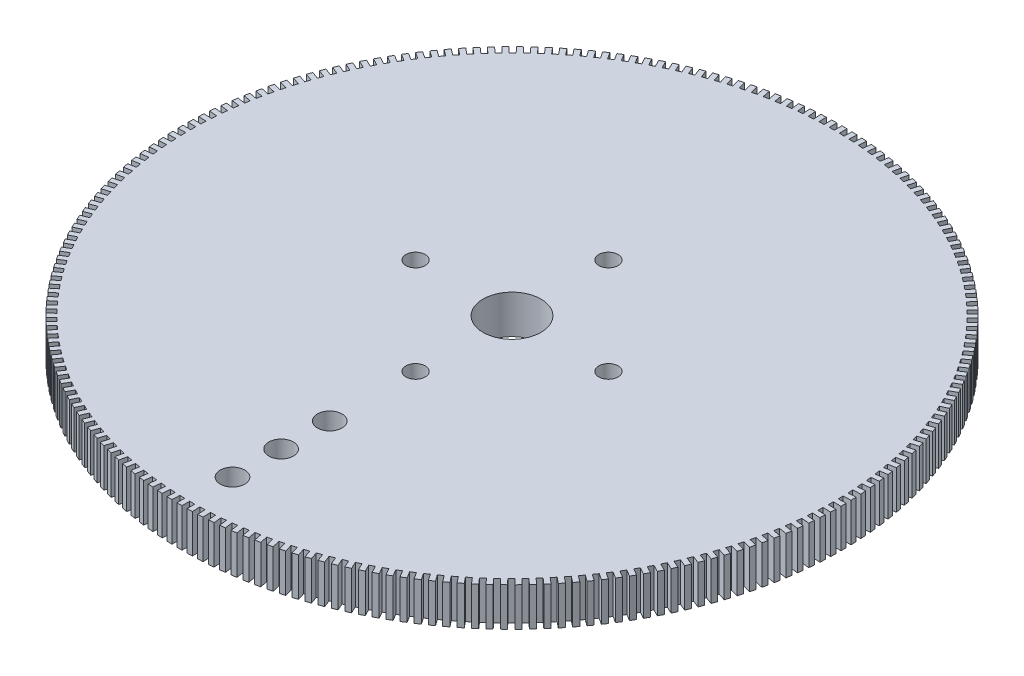
SolidWorks part; units mm, degrees
ref_plane "前基準面" through (0, 0, 0) normal (0, 0, 1) x (1, 0, 0)
ref_plane "上基準面" through (0, 0, 0) normal (0, 1, 0) x (1, 0, 0)
ref_plane "右基準面" through (0, 0, 0) normal (1, 0, 0) x (0, 0, -1)
sketch "草圖1" plane through (0, 0, 0) normal (0, 1, 0) x (1, 0, 0)
  circle A0 centre (0, 0) radius 54.229
  dimension "D1" = 108.458
extrude "填料-伸長1" add sketch "草圖1" along normal blind 6.35
sketch "草圖2" plane through (0, 6.35, 0) normal (0, 1, 0) x (1, 0, 0)
  circle A0 centre (0, 0) radius 4.7625
  circle A1 centre (-15.875, 0) radius 1.5875
  circle A2 centre (15.875, 0) radius 1.5875
  circle A3 centre (0, 15.875) radius 1.5875
  circle A4 centre (0, -15.875) radius 1.5875
  dimension "D1" = 9.525
  dimension "D2" = 3.175
  dimension "D3" = 3.175
  dimension "D4" = 3.175
  dimension "D5" = 3.175
  dimension "D6" = 15.875
  dimension "D7" = 15.875
  dimension "D8" = 15.875
  dimension "D9" = 15.875
extrude "除料-伸長1" cut sketch "草圖2" against normal blind 6.35
sketch "草圖4" plane through (0, 6.35, 0) normal (0, 1, 0) x (1, 0, 0)
  line L0 (0, 0) -> (-100.747, 10.3776) construction
  line L1 (0, 0) -> (-66.515, 6.3317) construction
  line L2 (0, 0) -> (-69.3079, 7.6816) construction
  line L3 (-52.7207, 5.0186) -> (-54.6004, 5.1975)
  line L4 (-54.6004, 5.1975) -> (-54.5069, 6.0411)
  line L5 (-54.5069, 6.0411) -> (-52.6367, 5.8339)
  line L6 (-52.5391, 6.6558) -> (-54.4123, 6.8931)
  line L7 (-54.4123, 6.8931) -> (-54.2926, 7.7334)
  line L8 (-54.2926, 7.7334) -> (-52.4298, 7.468)
  line L9 (-52.3067, 8.2865) -> (-54.1716, 8.582)
  line L10 (-54.1716, 8.582) -> (-54.0259, 9.4181)
  line L11 (-54.0259, 9.4181) -> (-52.1722, 9.095)
  line L12 (-52.0237, 9.9092) -> (-53.8785, 10.2626)
  line L13 (-53.8785, 10.2626) -> (-53.7068, 11.0938)
  line L14 (-53.7068, 11.0938) -> (-51.8641, 10.7131)
  line L15 (-51.6903, 11.5224) -> (-53.5333, 11.9332)
  line L16 (-53.5333, 11.9332) -> (-53.3358, 12.7587)
  line L17 (-53.3358, 12.7587) -> (-51.5058, 12.3209)
  line L18 (-51.307, 13.1244) -> (-53.1363, 13.5923)
  line L19 (-53.1363, 13.5923) -> (-52.9133, 14.4113)
  line L20 (-52.9133, 14.4113) -> (-51.0977, 13.9168)
  line L21 (-50.874, 14.7137) -> (-52.6879, 15.2383)
  line L22 (-52.6879, 15.2383) -> (-52.4395, 16.0499)
  line L23 (-52.4395, 16.0499) -> (-50.6402, 15.4992)
  line L24 (-50.3918, 16.2887) -> (-52.1885, 16.8695)
  line L25 (-52.1885, 16.8695) -> (-51.915, 17.673)
  line L26 (-51.915, 17.673) -> (-50.1337, 17.0666)
  line L27 (-49.8608, 17.848) -> (-51.6386, 18.4844)
  line L28 (-51.6386, 18.4844) -> (-51.3402, 19.279)
  line L29 (-51.3402, 19.279) -> (-49.5787, 18.6175)
  line L30 (-49.2817, 19.39) -> (-51.0388, 20.0814)
  line L31 (-51.0388, 20.0814) -> (-50.7158, 20.8663)
  line L32 (-50.7158, 20.8663) -> (-48.9757, 20.1504)
  line L33 (-48.6548, 20.9133) -> (-50.3895, 21.659)
  line L34 (-50.3895, 21.659) -> (-50.0423, 22.4335)
  line L35 (-50.0423, 22.4335) -> (-48.3253, 21.6638)
  line L36 (-47.9809, 22.4164) -> (-49.6916, 23.2156)
  line L37 (-49.6916, 23.2156) -> (-49.3205, 23.9789)
  line L38 (-49.3205, 23.9789) -> (-47.6282, 23.1562)
  line L39 (-47.2605, 23.8977) -> (-48.9455, 24.7498)
  line L40 (-48.9455, 24.7498) -> (-48.5509, 25.5012)
  line L41 (-48.5509, 25.5012) -> (-46.885, 24.6262)
  line L42 (-46.4944, 25.356) -> (-48.1521, 26.26)
  line L43 (-48.1521, 26.26) -> (-47.7343, 26.9988)
  line L44 (-47.7343, 26.9988) -> (-46.0965, 26.0724)
  line L45 (-45.6834, 26.7897) -> (-47.3122, 27.7448)
  line L46 (-47.3122, 27.7448) -> (-46.8715, 28.4703)
  line L47 (-46.8715, 28.4703) -> (-45.2633, 27.4934)
  line L48 (-44.8281, 28.1974) -> (-46.4264, 29.2028)
  line L49 (-46.4264, 29.2028) -> (-45.9634, 29.9142)
  line L50 (-45.9634, 29.9142) -> (-44.3864, 28.8878)
  line L51 (-43.9295, 29.578) -> (-45.4958, 30.6325)
  line L52 (-45.4958, 30.6325) -> (-45.0109, 31.3292)
  line L53 (-45.0109, 31.3292) -> (-43.4665, 30.2542)
  line L54 (-42.9884, 30.9298) -> (-44.5211, 32.0326)
  line L55 (-44.5211, 32.0326) -> (-44.0148, 32.7138)
  line L56 (-44.0148, 32.7138) -> (-42.5046, 31.5914)
  line L57 (-42.0057, 32.2518) -> (-43.5033, 33.4017)
  line L58 (-43.5033, 33.4017) -> (-42.9761, 34.0669)
  line L59 (-42.9761, 34.0669) -> (-41.5015, 32.898)
  line L60 (-40.9823, 33.5426) -> (-42.4435, 34.7385)
  line L61 (-42.4435, 34.7385) -> (-41.8958, 35.387)
  line L62 (-41.8958, 35.387) -> (-40.4583, 34.1728)
  line L63 (-39.9193, 34.8009) -> (-41.3426, 36.0417)
  line L64 (-41.3426, 36.0417) -> (-40.775, 36.6728)
  line L65 (-40.775, 36.6728) -> (-39.376, 35.4145)
  line L66 (-38.8177, 36.0256) -> (-40.2017, 37.31)
  line L67 (-40.2017, 37.31) -> (-39.6148, 37.9231)
  line L68 (-39.6148, 37.9231) -> (-38.2556, 36.622)
  line L69 (-37.6785, 37.2154) -> (-39.0219, 38.5422)
  line L70 (-39.0219, 38.5422) -> (-38.4162, 39.1368)
  line L71 (-38.4162, 39.1368) -> (-37.0981, 37.794)
  line L72 (-36.5029, 38.3692) -> (-37.8044, 39.7372)
  line L73 (-37.8044, 39.7372) -> (-37.1805, 40.3126)
  line L74 (-37.1805, 40.3126) -> (-35.9048, 38.9295)
  line L75 (-35.292, 39.4858) -> (-36.5503, 40.8937)
  line L76 (-36.5503, 40.8937) -> (-35.9088, 41.4494)
  line L77 (-35.9088, 41.4494) -> (-34.6767, 40.0273)
  line L78 (-34.0469, 40.5643) -> (-35.2608, 42.0106)
  line L79 (-35.2608, 42.0106) -> (-34.6023, 42.5461)
  line L80 (-34.6023, 42.5461) -> (-33.4151, 41.0863)
  line L81 (-32.7689, 41.6035) -> (-33.9373, 43.0869)
  line L82 (-33.9373, 43.0869) -> (-33.2624, 43.6017)
  line L83 (-33.2624, 43.6017) -> (-32.1212, 42.1057)
  line L84 (-31.4592, 42.6025) -> (-32.5808, 44.1215)
  line L85 (-32.5808, 44.1215) -> (-31.8903, 44.6151)
  line L86 (-31.8903, 44.6151) -> (-30.7961, 43.0843)
  line L87 (-30.119, 43.5603) -> (-31.1929, 45.1134)
  line L88 (-31.1929, 45.1134) -> (-30.4874, 45.5853)
  line L89 (-30.4874, 45.5853) -> (-29.4413, 44.0212)
  line L90 (-28.7498, 44.4759) -> (-29.7748, 46.0617)
  line L91 (-29.7748, 46.0617) -> (-29.0549, 46.5114)
  line L92 (-29.0549, 46.5114) -> (-28.058, 44.9155)
  line L93 (-27.3527, 45.3485) -> (-28.3279, 46.9654)
  line L94 (-28.3279, 46.9654) -> (-27.5944, 47.3925)
  line L95 (-27.5944, 47.3925) -> (-26.6476, 45.7664)
  line L96 (-25.9291, 46.1772) -> (-26.8536, 47.8237)
  line L97 (-26.8536, 47.8237) -> (-26.1071, 48.2277)
  line L98 (-26.1071, 48.2277) -> (-25.2114, 46.573)
  line L99 (-24.4804, 46.9613) -> (-25.3533, 48.6357)
  line L100 (-25.3533, 48.6357) -> (-24.5946, 49.0163)
  line L101 (-24.5946, 49.0163) -> (-23.7508, 47.3345)
  line L102 (-23.0081, 47.6999) -> (-23.8284, 49.4006)
  line L103 (-23.8284, 49.4006) -> (-23.0583, 49.7575)
  line L104 (-23.0583, 49.7575) -> (-22.2672, 48.0503)
  line L105 (-21.5135, 48.3924) -> (-22.2806, 50.1178)
  line L106 (-22.2806, 50.1178) -> (-21.4997, 50.4505)
  line L107 (-21.4997, 50.4505) -> (-20.7621, 48.7195)
  line L108 (-19.9981, 49.0381) -> (-20.7111, 50.7865)
  line L109 (-20.7111, 50.7865) -> (-19.9203, 51.0948)
  line L110 (-19.9203, 51.0948) -> (-19.2368, 49.3417)
  line L111 (-18.4634, 49.6363) -> (-19.1217, 51.406)
  line L112 (-19.1217, 51.406) -> (-18.3217, 51.6896)
  line L113 (-18.3217, 51.6896) -> (-17.693, 49.9161)
  line L114 (-16.9107, 50.1865) -> (-17.5137, 51.9758)
  line L115 (-17.5137, 51.9758) -> (-16.7053, 52.2344)
  line L116 (-16.7053, 52.2344) -> (-16.1321, 50.4422)
  line L117 (-15.3418, 50.6881) -> (-15.8888, 52.4954)
  line L118 (-15.8888, 52.4954) -> (-15.0727, 52.7287)
  line L119 (-15.0727, 52.7287) -> (-14.5555, 50.9195)
  line L120 (-13.758, 51.1407) -> (-14.2485, 52.9641)
  line L121 (-14.2485, 52.9641) -> (-13.4255, 53.1719)
  line L122 (-13.4255, 53.1719) -> (-12.9649, 51.3475)
  line L123 (-12.1608, 51.5439) -> (-12.5944, 53.3816)
  line L124 (-12.5944, 53.3816) -> (-11.7654, 53.5637)
  line L125 (-11.7654, 53.5637) -> (-11.3617, 51.7259)
  line L126 (-10.5519, 51.8971) -> (-10.9282, 53.7475)
  line L127 (-10.9282, 53.7475) -> (-10.0939, 53.9037)
  line L128 (-10.0939, 53.9037) -> (-9.7476, 52.0542)
  line L129 (-8.9329, 52.2002) -> (-9.2513, 54.0614)
  line L130 (-9.2513, 54.0614) -> (-8.4126, 54.1916)
  line L131 (-8.4126, 54.1916) -> (-8.124, 52.3322)
  line L132 (-7.3051, 52.4528) -> (-7.5656, 54.3229)
  line L133 (-7.5656, 54.3229) -> (-6.7232, 54.427)
  line L134 (-6.7232, 54.427) -> (-6.4925, 52.5595)
  line L135 (-5.6703, 52.6546) -> (-5.8725, 54.5319)
  line L136 (-5.8725, 54.5319) -> (-5.0273, 54.6097)
  line L137 (-5.0273, 54.6097) -> (-4.8548, 52.736)
  line L138 (-4.03, 52.8054) -> (-4.1737, 54.6882)
  line L139 (-4.1737, 54.6882) -> (-3.3265, 54.7397)
  line L140 (-3.3265, 54.7397) -> (-3.2124, 52.8615)
  line L141 (-2.3858, 52.9052) -> (-2.4709, 54.7915)
  line L142 (-2.4709, 54.7915) -> (-1.6225, 54.8166)
  line L143 (-1.6225, 54.8166) -> (-1.5668, 52.9358)
  line L144 (-0.7393, 52.9538) -> (-0.7657, 54.8419)
  line L145 (-0.7657, 54.8419) -> (0.0831, 54.8406)
  line L146 (0.0831, 54.8406) -> (0.0802, 52.9589)
  line L147 (0.9079, 52.9512) -> (0.9403, 54.8392)
  line L148 (0.9403, 54.8392) -> (1.7886, 54.8115)
  line L149 (1.7886, 54.8115) -> (1.7272, 52.9308)
  line L150 (2.5542, 52.8974) -> (2.6453, 54.7834)
  line L151 (2.6453, 54.7834) -> (3.4923, 54.7293)
  line L152 (3.4923, 54.7293) -> (3.3725, 52.8515)
  line L153 (4.1981, 52.7923) -> (4.3478, 54.6746)
  line L154 (4.3478, 54.6746) -> (5.1927, 54.5943)
  line L155 (5.1927, 54.5943) -> (5.0146, 52.7211)
  line L156 (5.8379, 52.6362) -> (6.046, 54.513)
  line L157 (6.046, 54.513) -> (6.8881, 54.4063)
  line L158 (6.8881, 54.4063) -> (6.6518, 52.5396)
  line L159 (7.4721, 52.4292) -> (7.7385, 54.2986)
  line L160 (7.7385, 54.2986) -> (8.5768, 54.1658)
  line L161 (8.5768, 54.1658) -> (8.2825, 52.3073)
  line L162 (9.099, 52.1715) -> (9.4234, 54.0316)
  line L163 (9.4234, 54.0316) -> (10.2572, 53.8729)
  line L164 (10.2572, 53.8729) -> (9.9053, 52.0244)
  line L165 (10.7171, 51.8633) -> (11.0992, 53.7124)
  line L166 (11.0992, 53.7124) -> (11.9277, 53.5278)
  line L167 (11.9277, 53.5278) -> (11.5184, 51.6912)
  line L168 (12.3249, 51.5049) -> (12.7643, 53.3413)
  line L169 (12.7643, 53.3413) -> (13.5866, 53.131)
  line L170 (13.5866, 53.131) -> (13.1204, 51.308)
  line L171 (13.9207, 51.0967) -> (14.417, 52.9185)
  line L172 (14.417, 52.9185) -> (15.2324, 52.6827)
  line L173 (15.2324, 52.6827) -> (14.7098, 50.8751)
  line L174 (15.5031, 50.639) -> (16.0558, 52.4445)
  line L175 (16.0558, 52.4445) -> (16.8635, 52.1835)
  line L176 (16.8635, 52.1835) -> (16.2849, 50.393)
  line L177 (17.0704, 50.1324) -> (17.6791, 51.9198)
  line L178 (17.6791, 51.9198) -> (18.4782, 51.6338)
  line L179 (18.4782, 51.6338) -> (17.8442, 49.8622)
  line L180 (18.6213, 49.5772) -> (19.2852, 51.3449)
  line L181 (19.2852, 51.3449) -> (20.0751, 51.0342)
  line L182 (20.0751, 51.0342) -> (19.3863, 49.2831)
  line L183 (20.1541, 48.9741) -> (20.8727, 50.7203)
  line L184 (20.8727, 50.7203) -> (21.6525, 50.3852)
  line L185 (21.6525, 50.3852) -> (20.9096, 48.6564)
  line L186 (21.6675, 48.3237) -> (22.44, 50.0466)
  line L187 (22.44, 50.0466) -> (23.209, 49.6874)
  line L188 (23.209, 49.6874) -> (22.4127, 47.9826)
  line L189 (23.1598, 47.6264) -> (23.9856, 49.3245)
  line L190 (23.9856, 49.3245) -> (24.7431, 48.9416)
  line L191 (24.7431, 48.9416) -> (23.8941, 47.2623)
  line L192 (24.6298, 46.8831) -> (25.508, 48.5547)
  line L193 (25.508, 48.5547) -> (26.2532, 48.1484)
  line L194 (26.2532, 48.1484) -> (25.3524, 46.4964)
  line L195 (26.076, 46.0945) -> (27.0057, 47.7379)
  line L196 (27.0057, 47.7379) -> (27.7379, 47.3086)
  line L197 (27.7379, 47.3086) -> (26.7862, 45.6854)
  line L198 (27.4969, 45.2612) -> (28.4773, 46.875)
  line L199 (28.4773, 46.875) -> (29.1958, 46.4231)
  line L200 (29.1958, 46.4231) -> (28.194, 44.8303)
  line L201 (28.8912, 44.3842) -> (29.9213, 45.9667)
  line L202 (29.9213, 45.9667) -> (30.6254, 45.4927)
  line L203 (30.6254, 45.4927) -> (29.5746, 43.9318)
  line L204 (30.2576, 43.4642) -> (31.3364, 45.0139)
  line L205 (31.3364, 45.0139) -> (32.0254, 44.5182)
  line L206 (32.0254, 44.5182) -> (30.9266, 42.9907)
  line L207 (31.5947, 42.5022) -> (32.7211, 44.0175)
  line L208 (32.7211, 44.0175) -> (33.3944, 43.5007)
  line L209 (33.3944, 43.5007) -> (32.2486, 42.0081)
  line L210 (32.9012, 41.499) -> (34.0743, 42.9786)
  line L211 (34.0743, 42.9786) -> (34.7311, 42.4411)
  line L212 (34.7311, 42.4411) -> (33.5394, 40.9849)
  line L213 (34.1759, 40.4557) -> (35.3944, 41.8981)
  line L214 (35.3944, 41.8981) -> (36.0342, 41.3404)
  line L215 (36.0342, 41.3404) -> (34.7978, 39.922)
  line L216 (35.4175, 39.3733) -> (36.6803, 40.7771)
  line L217 (36.6803, 40.7771) -> (37.3025, 40.1998)
  line L218 (37.3025, 40.1998) -> (36.0226, 38.8205)
  line L219 (36.6249, 38.2528) -> (37.9307, 39.6166)
  line L220 (37.9307, 39.6166) -> (38.5346, 39.0202)
  line L221 (38.5346, 39.0202) -> (37.2125, 37.6814)
  line L222 (37.7968, 37.0952) -> (39.1444, 38.4178)
  line L223 (39.1444, 38.4178) -> (39.7295, 37.8029)
  line L224 (39.7295, 37.8029) -> (38.3664, 36.5059)
  line L225 (38.9322, 35.9018) -> (40.3203, 37.1819)
  line L226 (40.3203, 37.1819) -> (40.886, 36.5491)
  line L227 (40.886, 36.5491) -> (39.4831, 35.295)
  line L228 (40.0299, 34.6736) -> (41.4571, 35.9099)
  line L229 (41.4571, 35.9099) -> (42.0029, 35.2598)
  line L230 (42.0029, 35.2598) -> (40.5617, 34.05)
  line L231 (41.0889, 33.412) -> (42.5539, 34.6032)
  line L232 (42.5539, 34.6032) -> (43.0791, 33.9365)
  line L233 (43.0791, 33.9365) -> (41.601, 32.7721)
  line L234 (42.1081, 32.1179) -> (43.6095, 33.2631)
  line L235 (43.6095, 33.2631) -> (44.1137, 32.5803)
  line L236 (44.1137, 32.5803) -> (42.6001, 31.4625)
  line L237 (43.0866, 30.7928) -> (44.6228, 31.8907)
  line L238 (44.6228, 31.8907) -> (45.1056, 31.1926)
  line L239 (45.1056, 31.1926) -> (43.558, 30.1224)
  line L240 (44.0234, 29.438) -> (45.5931, 30.4875)
  line L241 (45.5931, 30.4875) -> (46.0539, 29.7748)
  line L242 (46.0539, 29.7748) -> (44.4737, 28.7532)
  line L243 (44.9177, 28.0546) -> (46.5192, 29.0549)
  line L244 (46.5192, 29.0549) -> (46.9576, 28.3281)
  line L245 (46.9576, 28.3281) -> (45.3464, 27.3561)
  line L246 (45.7684, 26.6441) -> (47.4003, 27.5941)
  line L247 (47.4003, 27.5941) -> (47.8159, 26.854)
  line L248 (47.8159, 26.854) -> (46.1753, 25.9326)
  line L249 (46.5749, 25.2078) -> (48.2355, 26.1066)
  line L250 (48.2355, 26.1066) -> (48.6279, 25.354)
  line L251 (48.6279, 25.354) -> (46.9594, 24.484)
  line L252 (47.3363, 23.7471) -> (49.0241, 24.5938)
  line L253 (49.0241, 24.5938) -> (49.3929, 23.8294)
  line L254 (49.3929, 23.8294) -> (47.6982, 23.0118)
  line L255 (48.052, 22.2635) -> (49.7652, 23.0573)
  line L256 (49.7652, 23.0573) -> (50.1101, 22.2817)
  line L257 (50.1101, 22.2817) -> (48.3908, 21.5172)
  line L258 (48.7211, 20.7583) -> (50.4582, 21.4984)
  line L259 (50.4582, 21.4984) -> (50.7788, 20.7125)
  line L260 (50.7788, 20.7125) -> (49.0365, 20.0019)
  line L261 (49.3431, 19.2331) -> (51.1024, 19.9188)
  line L262 (51.1024, 19.9188) -> (51.3984, 19.1233)
  line L263 (51.3984, 19.1233) -> (49.6349, 18.4672)
  line L264 (49.9174, 17.6892) -> (51.6972, 18.3199)
  line L265 (51.6972, 18.3199) -> (51.9683, 17.5156)
  line L266 (51.9683, 17.5156) -> (50.1852, 16.9146)
  line L267 (50.4434, 16.1282) -> (52.2419, 16.7033)
  line L268 (52.2419, 16.7033) -> (52.4879, 15.8909)
  line L269 (52.4879, 15.8909) -> (50.6869, 15.3457)
  line L270 (50.9206, 14.5516) -> (52.7361, 15.0705)
  line L271 (52.7361, 15.0705) -> (52.9567, 14.2508)
  line L272 (52.9567, 14.2508) -> (51.1397, 13.7619)
  line L273 (51.3485, 12.961) -> (53.1793, 13.4231)
  line L274 (53.1793, 13.4231) -> (53.3743, 12.597)
  line L275 (53.3743, 12.597) -> (51.5429, 12.1648)
  line L276 (51.7268, 11.3578) -> (53.571, 11.7627)
  line L277 (53.571, 11.7627) -> (53.7402, 10.931)
  line L278 (53.7402, 10.931) -> (51.8963, 10.5559)
  line L279 (52.055, 9.7436) -> (53.9109, 10.091)
  line L280 (53.9109, 10.091) -> (54.0542, 9.2544)
  line L281 (54.0542, 9.2544) -> (52.1995, 8.9368)
  line L282 (52.3328, 8.12) -> (54.1987, 8.4095)
  line L283 (54.1987, 8.4095) -> (54.3158, 7.5688)
  line L284 (54.3158, 7.5688) -> (52.4522, 7.3091)
  line L285 (52.56, 6.4885) -> (54.434, 6.7198)
  line L286 (54.434, 6.7198) -> (54.5249, 5.8759)
  line L287 (54.5249, 5.8759) -> (52.6541, 5.6743)
  line L288 (52.7364, 4.8507) -> (54.6167, 5.0237)
  line L289 (54.6167, 5.0237) -> (54.6813, 4.1774)
  line L290 (54.6813, 4.1774) -> (52.8051, 4.0341)
  line L291 (52.8617, 3.2083) -> (54.7465, 3.3227)
  line L292 (54.7465, 3.3227) -> (54.7848, 2.4748)
  line L293 (54.7848, 2.4748) -> (52.905, 2.3899)
  line L294 (52.9359, 1.5628) -> (54.8233, 1.6185)
  line L295 (54.8233, 1.6185) -> (54.8352, 0.7698)
  line L296 (54.8352, 0.7698) -> (52.9538, 0.7434)
  line L297 (52.9589, -0.0843) -> (54.8471, -0.0873)
  line L298 (54.8471, -0.0873) -> (54.8327, -0.936)
  line L299 (54.8327, -0.936) -> (52.9513, -0.9038)
  line L300 (52.9307, -1.7313) -> (54.8179, -1.793)
  line L301 (54.8179, -1.793) -> (54.777, -2.6408)
  line L302 (54.777, -2.6408) -> (52.8976, -2.5502)
  line L303 (52.8512, -3.3766) -> (54.7356, -3.497)
  line L304 (54.7356, -3.497) -> (54.6684, -4.3431)
  line L305 (54.6684, -4.3431) -> (52.7927, -4.1941)
  line L306 (52.7207, -5.0186) -> (54.6004, -5.1975)
  line L307 (54.6004, -5.1975) -> (54.5069, -6.0411)
  line L308 (54.5069, -6.0411) -> (52.6367, -5.8339)
  line L309 (52.5391, -6.6558) -> (54.4123, -6.8931)
  line L310 (54.4123, -6.8931) -> (54.2926, -7.7334)
  line L311 (54.2926, -7.7334) -> (52.4298, -7.468)
  line L312 (52.3067, -8.2865) -> (54.1716, -8.582)
  line L313 (54.1716, -8.582) -> (54.0259, -9.4181)
  line L314 (54.0259, -9.4181) -> (52.1722, -9.095)
  line L315 (52.0237, -9.9092) -> (53.8785, -10.2626)
  line L316 (53.8785, -10.2626) -> (53.7068, -11.0938)
  line L317 (53.7068, -11.0938) -> (51.8641, -10.7131)
  line L318 (51.6903, -11.5224) -> (53.5333, -11.9332)
  line L319 (53.5333, -11.9332) -> (53.3358, -12.7587)
  line L320 (53.3358, -12.7587) -> (51.5058, -12.3209)
  line L321 (51.307, -13.1244) -> (53.1363, -13.5923)
  line L322 (53.1363, -13.5923) -> (52.9133, -14.4113)
  line L323 (52.9133, -14.4113) -> (51.0977, -13.9168)
  line L324 (50.874, -14.7137) -> (52.6879, -15.2383)
  line L325 (52.6879, -15.2383) -> (52.4395, -16.0499)
  line L326 (52.4395, -16.0499) -> (50.6402, -15.4992)
  line L327 (50.3918, -16.2887) -> (52.1885, -16.8695)
  line L328 (52.1885, -16.8695) -> (51.915, -17.673)
  line L329 (51.915, -17.673) -> (50.1337, -17.0666)
  line L330 (49.8608, -17.848) -> (51.6386, -18.4844)
  line L331 (51.6386, -18.4844) -> (51.3402, -19.279)
  line L332 (51.3402, -19.279) -> (49.5787, -18.6175)
  line L333 (49.2817, -19.39) -> (51.0388, -20.0814)
  line L334 (51.0388, -20.0814) -> (50.7158, -20.8663)
  line L335 (50.7158, -20.8663) -> (48.9757, -20.1504)
  line L336 (48.6548, -20.9133) -> (50.3895, -21.659)
  line L337 (50.3895, -21.659) -> (50.0423, -22.4335)
  line L338 (50.0423, -22.4335) -> (48.3253, -21.6638)
  line L339 (47.9809, -22.4164) -> (49.6916, -23.2156)
  line L340 (49.6916, -23.2156) -> (49.3205, -23.9789)
  line L341 (49.3205, -23.9789) -> (47.6282, -23.1562)
  line L342 (47.2605, -23.8977) -> (48.9455, -24.7498)
  line L343 (48.9455, -24.7498) -> (48.5509, -25.5012)
  line L344 (48.5509, -25.5012) -> (46.885, -24.6262)
  line L345 (46.4944, -25.356) -> (48.1521, -26.26)
  line L346 (48.1521, -26.26) -> (47.7343, -26.9988)
  line L347 (47.7343, -26.9988) -> (46.0965, -26.0724)
  line L348 (45.6834, -26.7897) -> (47.3122, -27.7448)
  line L349 (47.3122, -27.7448) -> (46.8715, -28.4703)
  line L350 (46.8715, -28.4703) -> (45.2633, -27.4934)
  line L351 (44.8281, -28.1974) -> (46.4264, -29.2028)
  line L352 (46.4264, -29.2028) -> (45.9634, -29.9142)
  line L353 (45.9634, -29.9142) -> (44.3864, -28.8878)
  line L354 (43.9295, -29.578) -> (45.4958, -30.6325)
  line L355 (45.4958, -30.6325) -> (45.0109, -31.3292)
  line L356 (45.0109, -31.3292) -> (43.4665, -30.2542)
  line L357 (42.9884, -30.9298) -> (44.5211, -32.0326)
  line L358 (44.5211, -32.0326) -> (44.0148, -32.7138)
  line L359 (44.0148, -32.7138) -> (42.5046, -31.5914)
  line L360 (42.0057, -32.2518) -> (43.5033, -33.4017)
  line L361 (43.5033, -33.4017) -> (42.9761, -34.0669)
  line L362 (42.9761, -34.0669) -> (41.5015, -32.898)
  line L363 (40.9823, -33.5426) -> (42.4435, -34.7385)
  line L364 (42.4435, -34.7385) -> (41.8958, -35.387)
  line L365 (41.8958, -35.387) -> (40.4583, -34.1728)
  line L366 (39.9193, -34.8009) -> (41.3426, -36.0417)
  line L367 (41.3426, -36.0417) -> (40.775, -36.6728)
  line L368 (40.775, -36.6728) -> (39.376, -35.4145)
  line L369 (38.8177, -36.0256) -> (40.2017, -37.31)
  line L370 (40.2017, -37.31) -> (39.6148, -37.9231)
  line L371 (39.6148, -37.9231) -> (38.2556, -36.622)
  line L372 (37.6785, -37.2154) -> (39.0219, -38.5422)
  line L373 (39.0219, -38.5422) -> (38.4162, -39.1368)
  line L374 (38.4162, -39.1368) -> (37.0981, -37.794)
  line L375 (36.5029, -38.3692) -> (37.8044, -39.7372)
  line L376 (37.8044, -39.7372) -> (37.1805, -40.3126)
  line L377 (37.1805, -40.3126) -> (35.9048, -38.9295)
  line L378 (35.292, -39.4858) -> (36.5503, -40.8937)
  line L379 (36.5503, -40.8937) -> (35.9088, -41.4494)
  line L380 (35.9088, -41.4494) -> (34.6767, -40.0273)
  line L381 (34.0469, -40.5643) -> (35.2608, -42.0106)
  line L382 (35.2608, -42.0106) -> (34.6023, -42.5461)
  line L383 (34.6023, -42.5461) -> (33.4151, -41.0863)
  line L384 (32.7689, -41.6035) -> (33.9373, -43.0869)
  line L385 (33.9373, -43.0869) -> (33.2624, -43.6017)
  line L386 (33.2624, -43.6017) -> (32.1212, -42.1057)
  line L387 (31.4592, -42.6025) -> (32.5808, -44.1215)
  line L388 (32.5808, -44.1215) -> (31.8903, -44.6151)
  line L389 (31.8903, -44.6151) -> (30.7961, -43.0843)
  line L390 (30.119, -43.5603) -> (31.1929, -45.1134)
  line L391 (31.1929, -45.1134) -> (30.4874, -45.5853)
  line L392 (30.4874, -45.5853) -> (29.4413, -44.0212)
  line L393 (28.7498, -44.4759) -> (29.7748, -46.0617)
  line L394 (29.7748, -46.0617) -> (29.0549, -46.5114)
  line L395 (29.0549, -46.5114) -> (28.058, -44.9155)
  line L396 (27.3527, -45.3485) -> (28.3279, -46.9654)
  line L397 (28.3279, -46.9654) -> (27.5944, -47.3925)
  line L398 (27.5944, -47.3925) -> (26.6476, -45.7664)
  line L399 (25.9291, -46.1772) -> (26.8536, -47.8237)
  line L400 (26.8536, -47.8237) -> (26.1071, -48.2277)
  line L401 (26.1071, -48.2277) -> (25.2114, -46.573)
  line L402 (24.4804, -46.9613) -> (25.3533, -48.6357)
  line L403 (25.3533, -48.6357) -> (24.5946, -49.0163)
  line L404 (24.5946, -49.0163) -> (23.7508, -47.3345)
  line L405 (23.0081, -47.6999) -> (23.8284, -49.4006)
  line L406 (23.8284, -49.4006) -> (23.0583, -49.7575)
  line L407 (23.0583, -49.7575) -> (22.2672, -48.0503)
  line L408 (21.5135, -48.3924) -> (22.2806, -50.1178)
  line L409 (22.2806, -50.1178) -> (21.4997, -50.4505)
  line L410 (21.4997, -50.4505) -> (20.7621, -48.7195)
  line L411 (19.9981, -49.0381) -> (20.7111, -50.7865)
  line L412 (20.7111, -50.7865) -> (19.9203, -51.0948)
  line L413 (19.9203, -51.0948) -> (19.2368, -49.3417)
  line L414 (18.4634, -49.6363) -> (19.1217, -51.406)
  line L415 (19.1217, -51.406) -> (18.3217, -51.6896)
  line L416 (18.3217, -51.6896) -> (17.693, -49.9161)
  line L417 (16.9107, -50.1865) -> (17.5137, -51.9758)
  line L418 (17.5137, -51.9758) -> (16.7053, -52.2344)
  line L419 (16.7053, -52.2344) -> (16.1321, -50.4422)
  line L420 (15.3418, -50.6881) -> (15.8888, -52.4954)
  line L421 (15.8888, -52.4954) -> (15.0727, -52.7287)
  line L422 (15.0727, -52.7287) -> (14.5555, -50.9195)
  line L423 (13.758, -51.1407) -> (14.2485, -52.9641)
  line L424 (14.2485, -52.9641) -> (13.4255, -53.1719)
  line L425 (13.4255, -53.1719) -> (12.9649, -51.3475)
  line L426 (12.1608, -51.5439) -> (12.5944, -53.3816)
  line L427 (12.5944, -53.3816) -> (11.7654, -53.5637)
  line L428 (11.7654, -53.5637) -> (11.3617, -51.7259)
  line L429 (10.5519, -51.8971) -> (10.9282, -53.7475)
  line L430 (10.9282, -53.7475) -> (10.0939, -53.9037)
  line L431 (10.0939, -53.9037) -> (9.7476, -52.0542)
  line L432 (8.9329, -52.2002) -> (9.2513, -54.0614)
  line L433 (9.2513, -54.0614) -> (8.4126, -54.1916)
  line L434 (8.4126, -54.1916) -> (8.124, -52.3322)
  line L435 (7.3051, -52.4528) -> (7.5656, -54.3229)
  line L436 (7.5656, -54.3229) -> (6.7232, -54.427)
  line L437 (6.7232, -54.427) -> (6.4925, -52.5595)
  line L438 (5.6703, -52.6546) -> (5.8725, -54.5319)
  line L439 (5.8725, -54.5319) -> (5.0273, -54.6097)
  line L440 (5.0273, -54.6097) -> (4.8548, -52.736)
  line L441 (4.03, -52.8054) -> (4.1737, -54.6882)
  line L442 (4.1737, -54.6882) -> (3.3265, -54.7397)
  line L443 (3.3265, -54.7397) -> (3.2124, -52.8615)
  line L444 (2.3858, -52.9052) -> (2.4709, -54.7915)
  line L445 (2.4709, -54.7915) -> (1.6225, -54.8166)
  line L446 (1.6225, -54.8166) -> (1.5668, -52.9358)
  line L447 (0.7393, -52.9538) -> (0.7657, -54.8419)
  line L448 (0.7657, -54.8419) -> (-0.0831, -54.8406)
  line L449 (-0.0831, -54.8406) -> (-0.0802, -52.9589)
  line L450 (-0.9079, -52.9512) -> (-0.9403, -54.8392)
  line L451 (-0.9403, -54.8392) -> (-1.7886, -54.8115)
  line L452 (-1.7886, -54.8115) -> (-1.7272, -52.9308)
  line L453 (-2.5542, -52.8974) -> (-2.6453, -54.7834)
  line L454 (-2.6453, -54.7834) -> (-3.4923, -54.7293)
  line L455 (-3.4923, -54.7293) -> (-3.3725, -52.8515)
  line L456 (-4.1981, -52.7923) -> (-4.3478, -54.6746)
  line L457 (-4.3478, -54.6746) -> (-5.1927, -54.5943)
  line L458 (-5.1927, -54.5943) -> (-5.0146, -52.7211)
  line L459 (-5.8379, -52.6362) -> (-6.046, -54.513)
  line L460 (-6.046, -54.513) -> (-6.8881, -54.4063)
  line L461 (-6.8881, -54.4063) -> (-6.6518, -52.5396)
  line L462 (-7.4721, -52.4292) -> (-7.7385, -54.2986)
  line L463 (-7.7385, -54.2986) -> (-8.5768, -54.1658)
  line L464 (-8.5768, -54.1658) -> (-8.2825, -52.3073)
  line L465 (-9.099, -52.1715) -> (-9.4234, -54.0316)
  line L466 (-9.4234, -54.0316) -> (-10.2572, -53.8729)
  line L467 (-10.2572, -53.8729) -> (-9.9053, -52.0244)
  line L468 (-10.7171, -51.8633) -> (-11.0992, -53.7124)
  line L469 (-11.0992, -53.7124) -> (-11.9277, -53.5278)
  line L470 (-11.9277, -53.5278) -> (-11.5184, -51.6912)
  line L471 (-12.3249, -51.5049) -> (-12.7643, -53.3413)
  line L472 (-12.7643, -53.3413) -> (-13.5866, -53.131)
  line L473 (-13.5866, -53.131) -> (-13.1204, -51.308)
  line L474 (-13.9207, -51.0967) -> (-14.417, -52.9185)
  line L475 (-14.417, -52.9185) -> (-15.2324, -52.6827)
  line L476 (-15.2324, -52.6827) -> (-14.7098, -50.8751)
  line L477 (-15.5031, -50.639) -> (-16.0558, -52.4445)
  line L478 (-16.0558, -52.4445) -> (-16.8635, -52.1835)
  line L479 (-16.8635, -52.1835) -> (-16.2849, -50.393)
  line L480 (-17.0704, -50.1324) -> (-17.6791, -51.9198)
  line L481 (-17.6791, -51.9198) -> (-18.4782, -51.6338)
  line L482 (-18.4782, -51.6338) -> (-17.8442, -49.8622)
  line L483 (-18.6213, -49.5772) -> (-19.2852, -51.3449)
  line L484 (-19.2852, -51.3449) -> (-20.0751, -51.0342)
  line L485 (-20.0751, -51.0342) -> (-19.3863, -49.2831)
  line L486 (-20.1541, -48.9741) -> (-20.8727, -50.7203)
  line L487 (-20.8727, -50.7203) -> (-21.6525, -50.3852)
  line L488 (-21.6525, -50.3852) -> (-20.9096, -48.6564)
  line L489 (-21.6675, -48.3237) -> (-22.44, -50.0466)
  line L490 (-22.44, -50.0466) -> (-23.209, -49.6874)
  line L491 (-23.209, -49.6874) -> (-22.4127, -47.9826)
  line L492 (-23.1598, -47.6264) -> (-23.9856, -49.3245)
  line L493 (-23.9856, -49.3245) -> (-24.7431, -48.9416)
  line L494 (-24.7431, -48.9416) -> (-23.8941, -47.2623)
  line L495 (-24.6298, -46.8831) -> (-25.508, -48.5547)
  line L496 (-25.508, -48.5547) -> (-26.2532, -48.1484)
  line L497 (-26.2532, -48.1484) -> (-25.3524, -46.4964)
  line L498 (-26.076, -46.0945) -> (-27.0057, -47.7379)
  line L499 (-27.0057, -47.7379) -> (-27.7379, -47.3086)
  line L500 (-27.7379, -47.3086) -> (-26.7862, -45.6854)
  line L501 (-27.4969, -45.2612) -> (-28.4773, -46.875)
  line L502 (-28.4773, -46.875) -> (-29.1958, -46.4231)
  line L503 (-29.1958, -46.4231) -> (-28.194, -44.8303)
  line L504 (-28.8912, -44.3842) -> (-29.9213, -45.9667)
  line L505 (-29.9213, -45.9667) -> (-30.6254, -45.4927)
  line L506 (-30.6254, -45.4927) -> (-29.5746, -43.9318)
  line L507 (-30.2576, -43.4642) -> (-31.3364, -45.0139)
  line L508 (-31.3364, -45.0139) -> (-32.0254, -44.5182)
  line L509 (-32.0254, -44.5182) -> (-30.9266, -42.9907)
  line L510 (-31.5947, -42.5022) -> (-32.7211, -44.0175)
  line L511 (-32.7211, -44.0175) -> (-33.3944, -43.5007)
  line L512 (-33.3944, -43.5007) -> (-32.2486, -42.0081)
  line L513 (-32.9012, -41.499) -> (-34.0743, -42.9786)
  line L514 (-34.0743, -42.9786) -> (-34.7311, -42.4411)
  line L515 (-34.7311, -42.4411) -> (-33.5394, -40.9849)
  line L516 (-34.1759, -40.4557) -> (-35.3944, -41.8981)
  line L517 (-35.3944, -41.8981) -> (-36.0342, -41.3404)
  line L518 (-36.0342, -41.3404) -> (-34.7978, -39.922)
  line L519 (-35.4175, -39.3733) -> (-36.6803, -40.7771)
  line L520 (-36.6803, -40.7771) -> (-37.3025, -40.1998)
  line L521 (-37.3025, -40.1998) -> (-36.0226, -38.8205)
  line L522 (-36.6249, -38.2528) -> (-37.9307, -39.6166)
  line L523 (-37.9307, -39.6166) -> (-38.5346, -39.0202)
  line L524 (-38.5346, -39.0202) -> (-37.2125, -37.6814)
  line L525 (-37.7968, -37.0952) -> (-39.1444, -38.4178)
  line L526 (-39.1444, -38.4178) -> (-39.7295, -37.8029)
  line L527 (-39.7295, -37.8029) -> (-38.3664, -36.5059)
  line L528 (-38.9322, -35.9018) -> (-40.3203, -37.1819)
  line L529 (-40.3203, -37.1819) -> (-40.886, -36.5491)
  line L530 (-40.886, -36.5491) -> (-39.4831, -35.295)
  line L531 (-40.0299, -34.6736) -> (-41.4571, -35.9099)
  line L532 (-41.4571, -35.9099) -> (-42.0029, -35.2598)
  line L533 (-42.0029, -35.2598) -> (-40.5617, -34.05)
  line L534 (-41.0889, -33.412) -> (-42.5539, -34.6032)
  line L535 (-42.5539, -34.6032) -> (-43.0791, -33.9365)
  line L536 (-43.0791, -33.9365) -> (-41.601, -32.7721)
  line L537 (-42.1081, -32.1179) -> (-43.6095, -33.2631)
  line L538 (-43.6095, -33.2631) -> (-44.1137, -32.5803)
  line L539 (-44.1137, -32.5803) -> (-42.6001, -31.4625)
  line L540 (-43.0866, -30.7928) -> (-44.6228, -31.8907)
  line L541 (-44.6228, -31.8907) -> (-45.1056, -31.1926)
  line L542 (-45.1056, -31.1926) -> (-43.558, -30.1224)
  line L543 (-44.0234, -29.438) -> (-45.5931, -30.4875)
  line L544 (-45.5931, -30.4875) -> (-46.0539, -29.7748)
  line L545 (-46.0539, -29.7748) -> (-44.4737, -28.7532)
  line L546 (-44.9177, -28.0546) -> (-46.5192, -29.0549)
  line L547 (-46.5192, -29.0549) -> (-46.9576, -28.3281)
  line L548 (-46.9576, -28.3281) -> (-45.3464, -27.3561)
  line L549 (-45.7684, -26.6441) -> (-47.4003, -27.5941)
  line L550 (-47.4003, -27.5941) -> (-47.8159, -26.854)
  line L551 (-47.8159, -26.854) -> (-46.1753, -25.9326)
  line L552 (-46.5749, -25.2078) -> (-48.2355, -26.1066)
  line L553 (-48.2355, -26.1066) -> (-48.6279, -25.354)
  line L554 (-48.6279, -25.354) -> (-46.9594, -24.484)
  line L555 (-47.3363, -23.7471) -> (-49.0241, -24.5938)
  line L556 (-49.0241, -24.5938) -> (-49.3929, -23.8294)
  line L557 (-49.3929, -23.8294) -> (-47.6982, -23.0118)
  line L558 (-48.052, -22.2635) -> (-49.7652, -23.0573)
  line L559 (-49.7652, -23.0573) -> (-50.1101, -22.2817)
  line L560 (-50.1101, -22.2817) -> (-48.3908, -21.5172)
  line L561 (-48.7211, -20.7583) -> (-50.4582, -21.4984)
  line L562 (-50.4582, -21.4984) -> (-50.7788, -20.7125)
  line L563 (-50.7788, -20.7125) -> (-49.0365, -20.0019)
  line L564 (-49.3431, -19.2331) -> (-51.1024, -19.9188)
  line L565 (-51.1024, -19.9188) -> (-51.3984, -19.1233)
  line L566 (-51.3984, -19.1233) -> (-49.6349, -18.4672)
  line L567 (-49.9174, -17.6892) -> (-51.6972, -18.3199)
  line L568 (-51.6972, -18.3199) -> (-51.9683, -17.5156)
  line L569 (-51.9683, -17.5156) -> (-50.1852, -16.9146)
  line L570 (-50.4434, -16.1282) -> (-52.2419, -16.7033)
  line L571 (-52.2419, -16.7033) -> (-52.4879, -15.8909)
  line L572 (-52.4879, -15.8909) -> (-50.6869, -15.3457)
  line L573 (-50.9206, -14.5516) -> (-52.7361, -15.0705)
  line L574 (-52.7361, -15.0705) -> (-52.9567, -14.2508)
  line L575 (-52.9567, -14.2508) -> (-51.1397, -13.7619)
  line L576 (-51.3485, -12.961) -> (-53.1793, -13.4231)
  line L577 (-53.1793, -13.4231) -> (-53.3743, -12.597)
  line L578 (-53.3743, -12.597) -> (-51.5429, -12.1648)
  line L579 (-51.7268, -11.3578) -> (-53.571, -11.7627)
  line L580 (-53.571, -11.7627) -> (-53.7402, -10.931)
  line L581 (-53.7402, -10.931) -> (-51.8963, -10.5559)
  line L582 (-52.055, -9.7436) -> (-53.9109, -10.091)
  line L583 (-53.9109, -10.091) -> (-54.0542, -9.2544)
  line L584 (-54.0542, -9.2544) -> (-52.1995, -8.9368)
  line L585 (-52.3328, -8.12) -> (-54.1987, -8.4095)
  line L586 (-54.1987, -8.4095) -> (-54.3158, -7.5688)
  line L587 (-54.3158, -7.5688) -> (-52.4522, -7.3091)
  line L588 (-52.56, -6.4885) -> (-54.434, -6.7198)
  line L589 (-54.434, -6.7198) -> (-54.5249, -5.8759)
  line L590 (-54.5249, -5.8759) -> (-52.6541, -5.6743)
  line L591 (-52.7364, -4.8507) -> (-54.6167, -5.0237)
  line L592 (-54.6167, -5.0237) -> (-54.6813, -4.1774)
  line L593 (-54.6813, -4.1774) -> (-52.8051, -4.0341)
  line L594 (-52.8617, -3.2083) -> (-54.7465, -3.3227)
  line L595 (-54.7465, -3.3227) -> (-54.7848, -2.4748)
  line L596 (-54.7848, -2.4748) -> (-52.905, -2.3899)
  line L597 (-52.9359, -1.5628) -> (-54.8233, -1.6185)
  line L598 (-54.8233, -1.6185) -> (-54.8352, -0.7698)
  line L599 (-54.8352, -0.7698) -> (-52.9538, -0.7434)
  line L600 (-52.9589, 0.0843) -> (-54.8471, 0.0873)
  line L601 (-54.8471, 0.0873) -> (-54.8327, 0.936)
  line L602 (-54.8327, 0.936) -> (-52.9513, 0.9038)
  line L603 (-52.9307, 1.7313) -> (-54.8179, 1.793)
  line L604 (-54.8179, 1.793) -> (-54.777, 2.6408)
  line L605 (-54.777, 2.6408) -> (-52.8976, 2.5502)
  line L606 (-52.8512, 3.3766) -> (-54.7356, 3.497)
  line L607 (-54.7356, 3.497) -> (-54.6684, 4.3431)
  line L608 (-54.6684, 4.3431) -> (-52.7927, 4.1941)
  arc A0 (-52.6367, 5.8339) -> (-52.7207, 5.0186) centre (0, 0) ccw
  circle A2 centre (0, 0) radius 54.229 construction
  arc A3 (-52.4298, 7.468) -> (-52.5391, 6.6558) centre (0, 0) ccw
  arc A4 (-52.1722, 9.095) -> (-52.3067, 8.2865) centre (0, 0) ccw
  arc A5 (-51.8641, 10.7131) -> (-52.0237, 9.9092) centre (0, 0) ccw
  arc A6 (-51.5058, 12.3209) -> (-51.6903, 11.5224) centre (0, 0) ccw
  arc A7 (-51.0977, 13.9168) -> (-51.307, 13.1244) centre (0, 0) ccw
  arc A8 (-50.6402, 15.4992) -> (-50.874, 14.7137) centre (0, 0) ccw
  arc A9 (-50.1337, 17.0666) -> (-50.3918, 16.2887) centre (0, 0) ccw
  arc A10 (-49.5787, 18.6175) -> (-49.8608, 17.848) centre (0, 0) ccw
  arc A11 (-48.9757, 20.1504) -> (-49.2817, 19.39) centre (0, 0) ccw
  arc A12 (-48.3253, 21.6638) -> (-48.6548, 20.9133) centre (0, 0) ccw
  arc A13 (-47.6282, 23.1562) -> (-47.9809, 22.4164) centre (0, 0) ccw
  arc A14 (-46.885, 24.6262) -> (-47.2605, 23.8977) centre (0, 0) ccw
  arc A15 (-46.0965, 26.0724) -> (-46.4944, 25.356) centre (0, 0) ccw
  arc A16 (-45.2633, 27.4934) -> (-45.6834, 26.7897) centre (0, 0) ccw
  arc A17 (-44.3864, 28.8878) -> (-44.8281, 28.1974) centre (0, 0) ccw
  arc A18 (-43.4665, 30.2542) -> (-43.9295, 29.578) centre (0, 0) ccw
  arc A19 (-42.5046, 31.5914) -> (-42.9884, 30.9298) centre (0, 0) ccw
  arc A20 (-41.5015, 32.898) -> (-42.0057, 32.2518) centre (0, 0) ccw
  arc A21 (-40.4583, 34.1728) -> (-40.9823, 33.5426) centre (0, 0) ccw
  arc A22 (-39.376, 35.4145) -> (-39.9193, 34.8009) centre (0, 0) ccw
  arc A23 (-38.2556, 36.622) -> (-38.8177, 36.0256) centre (0, 0) ccw
  arc A24 (-37.0981, 37.794) -> (-37.6785, 37.2154) centre (0, 0) ccw
  arc A25 (-35.9048, 38.9295) -> (-36.5029, 38.3692) centre (0, 0) ccw
  arc A26 (-34.6767, 40.0273) -> (-35.292, 39.4858) centre (0, 0) ccw
  arc A27 (-33.4151, 41.0863) -> (-34.0469, 40.5643) centre (0, 0) ccw
  arc A28 (-32.1212, 42.1057) -> (-32.7689, 41.6035) centre (0, 0) ccw
  arc A29 (-30.7961, 43.0843) -> (-31.4592, 42.6025) centre (0, 0) ccw
  arc A30 (-29.4413, 44.0212) -> (-30.119, 43.5603) centre (0, 0) ccw
  arc A31 (-28.058, 44.9155) -> (-28.7498, 44.4759) centre (0, 0) ccw
  arc A32 (-26.6476, 45.7664) -> (-27.3527, 45.3485) centre (0, 0) ccw
  arc A33 (-25.2114, 46.573) -> (-25.9291, 46.1772) centre (0, 0) ccw
  arc A34 (-23.7508, 47.3345) -> (-24.4804, 46.9613) centre (0, 0) ccw
  arc A35 (-22.2672, 48.0503) -> (-23.0081, 47.6999) centre (0, 0) ccw
  arc A36 (-20.7621, 48.7195) -> (-21.5135, 48.3924) centre (0, 0) ccw
  arc A37 (-19.2368, 49.3417) -> (-19.9981, 49.0381) centre (0, 0) ccw
  arc A38 (-17.693, 49.9161) -> (-18.4634, 49.6363) centre (0, 0) ccw
  arc A39 (-16.1321, 50.4422) -> (-16.9107, 50.1865) centre (0, 0) ccw
  arc A40 (-14.5555, 50.9195) -> (-15.3418, 50.6881) centre (0, 0) ccw
  arc A41 (-12.9649, 51.3475) -> (-13.758, 51.1407) centre (0, 0) ccw
  arc A42 (-11.3617, 51.7259) -> (-12.1608, 51.5439) centre (0, 0) ccw
  arc A43 (-9.7476, 52.0542) -> (-10.5519, 51.8971) centre (0, 0) ccw
  arc A44 (-8.124, 52.3322) -> (-8.9329, 52.2002) centre (0, 0) ccw
  arc A45 (-6.4925, 52.5595) -> (-7.3051, 52.4528) centre (0, 0) ccw
  arc A46 (-4.8548, 52.736) -> (-5.6703, 52.6546) centre (0, 0) ccw
  arc A47 (-3.2124, 52.8615) -> (-4.03, 52.8054) centre (0, 0) ccw
  arc A48 (-1.5668, 52.9358) -> (-2.3858, 52.9052) centre (0, 0) ccw
  arc A49 (0.0802, 52.9589) -> (-0.7393, 52.9538) centre (0, 0) ccw
  arc A50 (1.7272, 52.9308) -> (0.9079, 52.9512) centre (0, 0) ccw
  arc A51 (3.3725, 52.8515) -> (2.5542, 52.8974) centre (0, 0) ccw
  arc A52 (5.0146, 52.7211) -> (4.1981, 52.7923) centre (0, 0) ccw
  arc A53 (6.6518, 52.5396) -> (5.8379, 52.6362) centre (0, 0) ccw
  arc A54 (8.2825, 52.3073) -> (7.4721, 52.4292) centre (0, 0) ccw
  arc A55 (9.9053, 52.0244) -> (9.099, 52.1715) centre (0, 0) ccw
  arc A56 (11.5184, 51.6912) -> (10.7171, 51.8633) centre (0, 0) ccw
  arc A57 (13.1204, 51.308) -> (12.3249, 51.5049) centre (0, 0) ccw
  arc A58 (14.7098, 50.8751) -> (13.9207, 51.0967) centre (0, 0) ccw
  arc A59 (16.2849, 50.393) -> (15.5031, 50.639) centre (0, 0) ccw
  arc A60 (17.8442, 49.8622) -> (17.0704, 50.1324) centre (0, 0) ccw
  arc A61 (19.3863, 49.2831) -> (18.6213, 49.5772) centre (0, 0) ccw
  arc A62 (20.9096, 48.6564) -> (20.1541, 48.9741) centre (0, 0) ccw
  arc A63 (22.4127, 47.9826) -> (21.6675, 48.3237) centre (0, 0) ccw
  arc A64 (23.8941, 47.2623) -> (23.1598, 47.6264) centre (0, 0) ccw
  arc A65 (25.3524, 46.4964) -> (24.6298, 46.8831) centre (0, 0) ccw
  arc A66 (26.7862, 45.6854) -> (26.076, 46.0945) centre (0, 0) ccw
  arc A67 (28.194, 44.8303) -> (27.4969, 45.2612) centre (0, 0) ccw
  arc A68 (29.5746, 43.9318) -> (28.8912, 44.3842) centre (0, 0) ccw
  arc A69 (30.9266, 42.9907) -> (30.2576, 43.4642) centre (0, 0) ccw
  arc A70 (32.2486, 42.0081) -> (31.5947, 42.5022) centre (0, 0) ccw
  arc A71 (33.5394, 40.9849) -> (32.9012, 41.499) centre (0, 0) ccw
  arc A72 (34.7978, 39.922) -> (34.1759, 40.4557) centre (0, 0) ccw
  arc A73 (36.0226, 38.8205) -> (35.4175, 39.3733) centre (0, 0) ccw
  arc A74 (37.2125, 37.6814) -> (36.6249, 38.2528) centre (0, 0) ccw
  arc A75 (38.3664, 36.5059) -> (37.7968, 37.0952) centre (0, 0) ccw
  arc A76 (39.4831, 35.295) -> (38.9322, 35.9018) centre (0, 0) ccw
  arc A77 (40.5617, 34.05) -> (40.0299, 34.6736) centre (0, 0) ccw
  arc A78 (41.601, 32.7721) -> (41.0889, 33.412) centre (0, 0) ccw
  arc A79 (42.6001, 31.4625) -> (42.1081, 32.1179) centre (0, 0) ccw
  arc A80 (43.558, 30.1224) -> (43.0866, 30.7928) centre (0, 0) ccw
  arc A81 (44.4737, 28.7532) -> (44.0234, 29.438) centre (0, 0) ccw
  arc A82 (45.3464, 27.3561) -> (44.9177, 28.0546) centre (0, 0) ccw
  arc A83 (46.1753, 25.9326) -> (45.7684, 26.6441) centre (0, 0) ccw
  arc A84 (46.9594, 24.484) -> (46.5749, 25.2078) centre (0, 0) ccw
  arc A85 (47.6982, 23.0118) -> (47.3363, 23.7471) centre (0, 0) ccw
  arc A86 (48.3908, 21.5172) -> (48.052, 22.2635) centre (0, 0) ccw
  arc A87 (49.0365, 20.0019) -> (48.7211, 20.7583) centre (0, 0) ccw
  arc A88 (49.6349, 18.4672) -> (49.3431, 19.2331) centre (0, 0) ccw
  arc A89 (50.1852, 16.9146) -> (49.9174, 17.6892) centre (0, 0) ccw
  arc A90 (50.6869, 15.3457) -> (50.4434, 16.1282) centre (0, 0) ccw
  arc A91 (51.1397, 13.7619) -> (50.9206, 14.5516) centre (0, 0) ccw
  arc A92 (51.5429, 12.1648) -> (51.3485, 12.961) centre (0, 0) ccw
  arc A93 (51.8963, 10.5559) -> (51.7268, 11.3578) centre (0, 0) ccw
  arc A94 (52.1995, 8.9368) -> (52.055, 9.7436) centre (0, 0) ccw
  arc A95 (52.4522, 7.3091) -> (52.3328, 8.12) centre (0, 0) ccw
  arc A96 (52.6541, 5.6743) -> (52.56, 6.4885) centre (0, 0) ccw
  arc A97 (52.8051, 4.0341) -> (52.7364, 4.8507) centre (0, 0) ccw
  arc A98 (52.905, 2.3899) -> (52.8617, 3.2083) centre (0, 0) ccw
  arc A99 (52.9538, 0.7434) -> (52.9359, 1.5628) centre (0, 0) ccw
  arc A100 (52.9513, -0.9038) -> (52.9589, -0.0843) centre (0, 0) ccw
  arc A101 (52.8976, -2.5502) -> (52.9307, -1.7313) centre (0, 0) ccw
  arc A102 (52.7927, -4.1941) -> (52.8512, -3.3766) centre (0, 0) ccw
  arc A103 (52.6367, -5.8339) -> (52.7207, -5.0186) centre (0, 0) ccw
  arc A104 (52.4298, -7.468) -> (52.5391, -6.6558) centre (0, 0) ccw
  arc A105 (52.1722, -9.095) -> (52.3067, -8.2865) centre (0, 0) ccw
  arc A106 (51.8641, -10.7131) -> (52.0237, -9.9092) centre (0, 0) ccw
  arc A107 (51.5058, -12.3209) -> (51.6903, -11.5224) centre (0, 0) ccw
  arc A108 (51.0977, -13.9168) -> (51.307, -13.1244) centre (0, 0) ccw
  arc A109 (50.6402, -15.4992) -> (50.874, -14.7137) centre (0, 0) ccw
  arc A110 (50.1337, -17.0666) -> (50.3918, -16.2887) centre (0, 0) ccw
  arc A111 (49.5787, -18.6175) -> (49.8608, -17.848) centre (0, 0) ccw
  arc A112 (48.9757, -20.1504) -> (49.2817, -19.39) centre (0, 0) ccw
  arc A113 (48.3253, -21.6638) -> (48.6548, -20.9133) centre (0, 0) ccw
  arc A114 (47.6282, -23.1562) -> (47.9809, -22.4164) centre (0, 0) ccw
  arc A115 (46.885, -24.6262) -> (47.2605, -23.8977) centre (0, 0) ccw
  arc A116 (46.0965, -26.0724) -> (46.4944, -25.356) centre (0, 0) ccw
  arc A117 (45.2633, -27.4934) -> (45.6834, -26.7897) centre (0, 0) ccw
  arc A118 (44.3864, -28.8878) -> (44.8281, -28.1974) centre (0, 0) ccw
  arc A119 (43.4665, -30.2542) -> (43.9295, -29.578) centre (0, 0) ccw
  arc A120 (42.5046, -31.5914) -> (42.9884, -30.9298) centre (0, 0) ccw
  arc A121 (41.5015, -32.898) -> (42.0057, -32.2518) centre (0, 0) ccw
  arc A122 (40.4583, -34.1728) -> (40.9823, -33.5426) centre (0, 0) ccw
  arc A123 (39.376, -35.4145) -> (39.9193, -34.8009) centre (0, 0) ccw
  arc A124 (38.2556, -36.622) -> (38.8177, -36.0256) centre (0, 0) ccw
  arc A125 (37.0981, -37.794) -> (37.6785, -37.2154) centre (0, 0) ccw
  arc A126 (35.9048, -38.9295) -> (36.5029, -38.3692) centre (0, 0) ccw
  arc A127 (34.6767, -40.0273) -> (35.292, -39.4858) centre (0, 0) ccw
  arc A128 (33.4151, -41.0863) -> (34.0469, -40.5643) centre (0, 0) ccw
  arc A129 (32.1212, -42.1057) -> (32.7689, -41.6035) centre (0, 0) ccw
  arc A130 (30.7961, -43.0843) -> (31.4592, -42.6025) centre (0, 0) ccw
  arc A131 (29.4413, -44.0212) -> (30.119, -43.5603) centre (0, 0) ccw
  arc A132 (28.058, -44.9155) -> (28.7498, -44.4759) centre (0, 0) ccw
  arc A133 (26.6476, -45.7664) -> (27.3527, -45.3485) centre (0, 0) ccw
  arc A134 (25.2114, -46.573) -> (25.9291, -46.1772) centre (0, 0) ccw
  arc A135 (23.7508, -47.3345) -> (24.4804, -46.9613) centre (0, 0) ccw
  arc A136 (22.2672, -48.0503) -> (23.0081, -47.6999) centre (0, 0) ccw
  arc A137 (20.7621, -48.7195) -> (21.5135, -48.3924) centre (0, 0) ccw
  arc A138 (19.2368, -49.3417) -> (19.9981, -49.0381) centre (0, 0) ccw
  arc A139 (17.693, -49.9161) -> (18.4634, -49.6363) centre (0, 0) ccw
  arc A140 (16.1321, -50.4422) -> (16.9107, -50.1865) centre (0, 0) ccw
  arc A141 (14.5555, -50.9195) -> (15.3418, -50.6881) centre (0, 0) ccw
  arc A142 (12.9649, -51.3475) -> (13.758, -51.1407) centre (0, 0) ccw
  arc A143 (11.3617, -51.7259) -> (12.1608, -51.5439) centre (0, 0) ccw
  arc A144 (9.7476, -52.0542) -> (10.5519, -51.8971) centre (0, 0) ccw
  arc A145 (8.124, -52.3322) -> (8.9329, -52.2002) centre (0, 0) ccw
  arc A146 (6.4925, -52.5595) -> (7.3051, -52.4528) centre (0, 0) ccw
  arc A147 (4.8548, -52.736) -> (5.6703, -52.6546) centre (0, 0) ccw
  arc A148 (3.2124, -52.8615) -> (4.03, -52.8054) centre (0, 0) ccw
  arc A149 (1.5668, -52.9358) -> (2.3858, -52.9052) centre (0, 0) ccw
  arc A150 (-0.0802, -52.9589) -> (0.7393, -52.9538) centre (0, 0) ccw
  arc A151 (-1.7272, -52.9308) -> (-0.9079, -52.9512) centre (0, 0) ccw
  arc A152 (-3.3725, -52.8515) -> (-2.5542, -52.8974) centre (0, 0) ccw
  arc A153 (-5.0146, -52.7211) -> (-4.1981, -52.7923) centre (0, 0) ccw
  arc A154 (-6.6518, -52.5396) -> (-5.8379, -52.6362) centre (0, 0) ccw
  arc A155 (-8.2825, -52.3073) -> (-7.4721, -52.4292) centre (0, 0) ccw
  arc A156 (-9.9053, -52.0244) -> (-9.099, -52.1715) centre (0, 0) ccw
  arc A157 (-11.5184, -51.6912) -> (-10.7171, -51.8633) centre (0, 0) ccw
  arc A158 (-13.1204, -51.308) -> (-12.3249, -51.5049) centre (0, 0) ccw
  arc A159 (-14.7098, -50.8751) -> (-13.9207, -51.0967) centre (0, 0) ccw
  arc A160 (-16.2849, -50.393) -> (-15.5031, -50.639) centre (0, 0) ccw
  arc A161 (-17.8442, -49.8622) -> (-17.0704, -50.1324) centre (0, 0) ccw
  arc A162 (-19.3863, -49.2831) -> (-18.6213, -49.5772) centre (0, 0) ccw
  arc A163 (-20.9096, -48.6564) -> (-20.1541, -48.9741) centre (0, 0) ccw
  arc A164 (-22.4127, -47.9826) -> (-21.6675, -48.3237) centre (0, 0) ccw
  arc A165 (-23.8941, -47.2623) -> (-23.1598, -47.6264) centre (0, 0) ccw
  arc A166 (-25.3524, -46.4964) -> (-24.6298, -46.8831) centre (0, 0) ccw
  arc A167 (-26.7862, -45.6854) -> (-26.076, -46.0945) centre (0, 0) ccw
  arc A168 (-28.194, -44.8303) -> (-27.4969, -45.2612) centre (0, 0) ccw
  arc A169 (-29.5746, -43.9318) -> (-28.8912, -44.3842) centre (0, 0) ccw
  arc A170 (-30.9266, -42.9907) -> (-30.2576, -43.4642) centre (0, 0) ccw
  arc A171 (-32.2486, -42.0081) -> (-31.5947, -42.5022) centre (0, 0) ccw
  arc A172 (-33.5394, -40.9849) -> (-32.9012, -41.499) centre (0, 0) ccw
  arc A173 (-34.7978, -39.922) -> (-34.1759, -40.4557) centre (0, 0) ccw
  arc A174 (-36.0226, -38.8205) -> (-35.4175, -39.3733) centre (0, 0) ccw
  arc A175 (-37.2125, -37.6814) -> (-36.6249, -38.2528) centre (0, 0) ccw
  arc A176 (-38.3664, -36.5059) -> (-37.7968, -37.0952) centre (0, 0) ccw
  arc A177 (-39.4831, -35.295) -> (-38.9322, -35.9018) centre (0, 0) ccw
  arc A178 (-40.5617, -34.05) -> (-40.0299, -34.6736) centre (0, 0) ccw
  arc A179 (-41.601, -32.7721) -> (-41.0889, -33.412) centre (0, 0) ccw
  arc A180 (-42.6001, -31.4625) -> (-42.1081, -32.1179) centre (0, 0) ccw
  arc A181 (-43.558, -30.1224) -> (-43.0866, -30.7928) centre (0, 0) ccw
  arc A182 (-44.4737, -28.7532) -> (-44.0234, -29.438) centre (0, 0) ccw
  arc A183 (-45.3464, -27.3561) -> (-44.9177, -28.0546) centre (0, 0) ccw
  arc A184 (-46.1753, -25.9326) -> (-45.7684, -26.6441) centre (0, 0) ccw
  arc A185 (-46.9594, -24.484) -> (-46.5749, -25.2078) centre (0, 0) ccw
  arc A186 (-47.6982, -23.0118) -> (-47.3363, -23.7471) centre (0, 0) ccw
  arc A187 (-48.3908, -21.5172) -> (-48.052, -22.2635) centre (0, 0) ccw
  arc A188 (-49.0365, -20.0019) -> (-48.7211, -20.7583) centre (0, 0) ccw
  arc A189 (-49.6349, -18.4672) -> (-49.3431, -19.2331) centre (0, 0) ccw
  arc A190 (-50.1852, -16.9146) -> (-49.9174, -17.6892) centre (0, 0) ccw
  arc A191 (-50.6869, -15.3457) -> (-50.4434, -16.1282) centre (0, 0) ccw
  arc A192 (-51.1397, -13.7619) -> (-50.9206, -14.5516) centre (0, 0) ccw
  arc A193 (-51.5429, -12.1648) -> (-51.3485, -12.961) centre (0, 0) ccw
  arc A194 (-51.8963, -10.5559) -> (-51.7268, -11.3578) centre (0, 0) ccw
  arc A195 (-52.1995, -8.9368) -> (-52.055, -9.7436) centre (0, 0) ccw
  arc A196 (-52.4522, -7.3091) -> (-52.3328, -8.12) centre (0, 0) ccw
  arc A197 (-52.6541, -5.6743) -> (-52.56, -6.4885) centre (0, 0) ccw
  arc A198 (-52.8051, -4.0341) -> (-52.7364, -4.8507) centre (0, 0) ccw
  arc A199 (-52.905, -2.3899) -> (-52.8617, -3.2083) centre (0, 0) ccw
  arc A200 (-52.9538, -0.7434) -> (-52.9359, -1.5628) centre (0, 0) ccw
  arc A201 (-52.9513, 0.9038) -> (-52.9589, 0.0843) centre (0, 0) ccw
  arc A202 (-52.8976, 2.5502) -> (-52.9307, 1.7313) centre (0, 0) ccw
  arc A203 (-52.7927, 4.1941) -> (-52.8512, 3.3766) centre (0, 0) ccw
  dimension "D1" = 1.27
  dimension "D4" = 202
  dimension "D2" = 0.443
  dimension "D3" = 0.443
extrude "除料-伸長2" cut sketch "草圖4" against normal blind 6.35
hole_wizard "#10-32 螺紋孔1" positions "草圖7" profile "草圖6" tap size "#10-32" standard "Ansi 英吋"
sketch "草圖7" plane through (0, 6.35, 0) normal (0, 1, 0) x (-1, 0, 0)
  line L0 (0, 0) -> (0, 15.875) construction
  line L1 (0, 15.875) -> (0, 76.125) construction
  point P0 (0, 46)
  point P10 (0, 38)
  point P13 (0, 30)
  dimension "D1" = 46
  dimension "D2" = 38
  dimension "D3" = 30
sketch "草圖6" plane through (0, 6.35, 46) normal (1, 0, 0) x (0, 0, 1)
  line L0 (0, 0) -> (0, 14.9293)
  line L1 (0, 14.9293) -> (2.0193, 13.716)
  line L2 (2.0193, 13.716) -> (2.0193, 0)
  line L5 (2.0193, 0) -> (0, 0)
  line L10 (0, 14.9293) -> (-2.0193, 13.716) construction
  line L11 (0, -6.35) -> (0, 107.95) construction
  dimension "螺孔鑽直徑" = 4.0386
  dimension "螺孔鑽深度" = 13.716
  dimension "導頭角度" = 118
cosmetic thread "鑽孔螺紋1" parameters "D1"=6.35, "D2"=4.826
cosmetic thread "鑽孔螺紋2" parameters "D1"=6.35, "D2"=4.826
cosmetic thread "鑽孔螺紋3" parameters "D1"=6.35, "D2"=4.826
